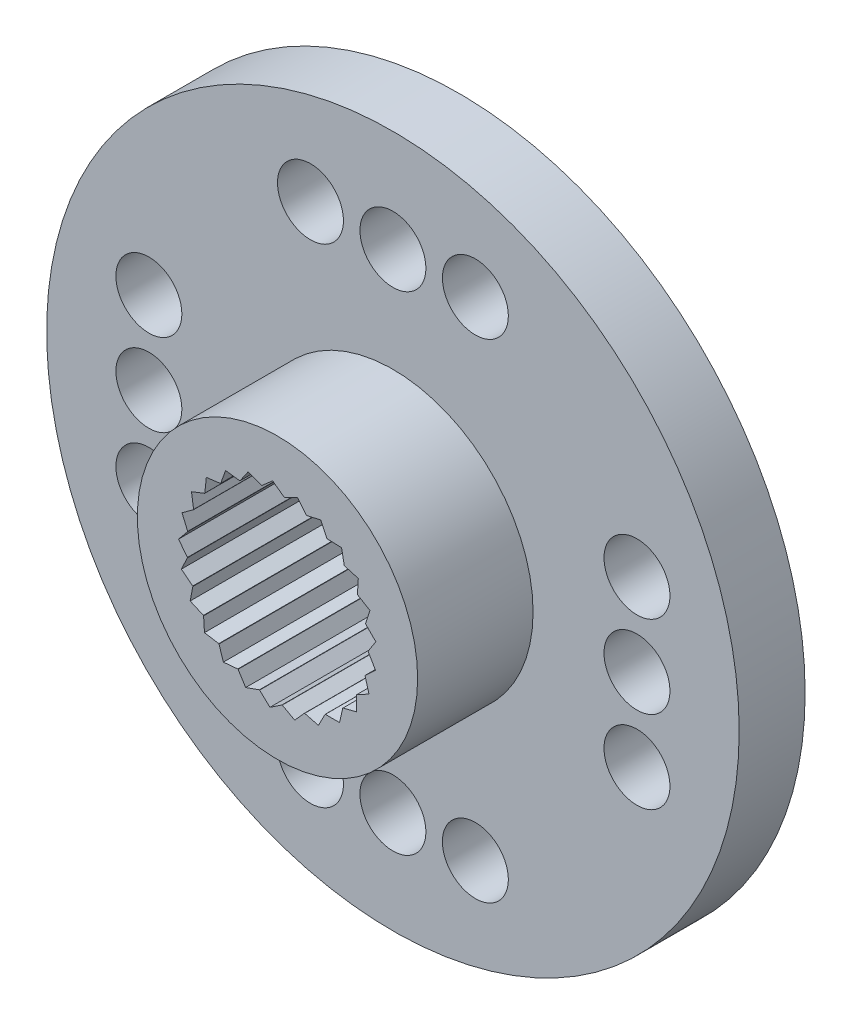
SolidWorks part; units mm, degrees
ref_plane "Front Plane" through (0, 0, 0) normal (0, 0, 1) x (1, 0, 0)
ref_plane "Top Plane" through (0, 0, 0) normal (0, 1, 0) x (1, 0, 0)
ref_plane "Right Plane" through (0, 0, 0) normal (1, 0, 0) x (0, 0, -1)
sketch "Sketch1" plane through (0, 0, 0) normal (0, 0, 1) x (1, 0, 0)
  circle A0 centre (0, 0) radius 10.5
  dimension "D1" = 21
extrude "Boss-Extrude1" add sketch "Sketch1" along normal blind 2
sketch "Sketch2" plane through (0, 0, 2) normal (0, 0, 1) x (1, 0, 0)
  circle A0 centre (0, 0) radius 4.25
  dimension "D1" = 8.5
extrude "Boss-Extrude2" add sketch "Sketch2" along normal blind 3.5
sketch "Sketch3" plane through (0, 0, 5.5) normal (0, 0, 1) x (1, 0, 0)
  circle A0 centre (0, 0) radius 2.75
  dimension "D1" = 5.5
extrude "Cut-Extrude1" cut sketch "Sketch3" against normal blind 4.5
sketch "Sketch4" plane through (0, 0, 0) normal (0, 0, 1) x (1, 0, 0)
  circle A0 centre (0, 0) radius 1.6
  dimension "D1" = 3.2
extrude "Cut-Extrude2" cut sketch "Sketch4" along normal blind 3.5
sketch "Sketch5" plane through (0, 0, 2) normal (0, 0, 1) x (1, 0, 0)
  line L0 (-10.5, 0) -> (10.5, 0) construction
  line L1 (-2.5, 7.4) -> (0, 7.4) construction
  line L2 (0, 7.4) -> (2.5, 7.4) construction
  line L3 (0, 7.4) -> (0, 0) construction
  line L4 (0, -7.4) -> (2.5, -7.4) construction
  line L5 (-2.5, -7.4) -> (0, -7.4) construction
  line L6 (7.4, 2.5) -> (7.4, 0) construction
  line L7 (7.4, 0) -> (7.4, -2.5) construction
  line L8 (-7.4, 0) -> (-7.4, -2.5) construction
  line L9 (-7.4, 2.5) -> (-7.4, 0) construction
  circle A0 centre (0, 7.4) radius 1
  circle A1 centre (-2.5, 7.4) radius 1
  circle A2 centre (2.5, 7.4) radius 1
  circle A3 centre (0, 0) radius 10.5 construction
  circle A4 centre (2.5, -7.4) radius 1
  circle A5 centre (-2.5, -7.4) radius 1
  circle A6 centre (0, -7.4) radius 1
  circle A7 centre (7.4, 0) radius 1
  circle A8 centre (7.4, 2.5) radius 1
  circle A9 centre (7.4, -2.5) radius 1
  circle A10 centre (-7.4, -2.5) radius 1
  circle A11 centre (-7.4, 2.5) radius 1
  circle A12 centre (-7.4, 0) radius 1
  dimension "D1" = 2
  dimension "D2" = 2
  dimension "D3" = 2
  dimension "D7" = 2
  dimension "D8" = 2
  dimension "D9" = 2
  dimension "D4" = 2.5
  dimension "D5" = 2.5
  dimension "D6" = 7.4
  dimension "D10" = 2.5
  dimension "D11" = 2.5
  dimension "D12" = 7.4
extrude "Cut-Extrude3" cut sketch "Sketch5" against normal blind 3.5
sketch "Sketch6" plane through (0, 0, 5.5) normal (0, 0, 1) x (1, 0, 0)
  line L0 (-0.9385, 2.5849) -> (-1.5278, 2.371)
  line L1 (0, 0) -> (-2.971, 0.4161)
  line L2 (0, 0) -> (-2.8954, 0.7852)
  line L3 (-2.8954, 0.7852) -> (-2.7234, 0.3814)
  line L4 (-2.8954, 0.7852) -> (-2.5466, 1.0378)
  line L5 (0, 0) -> (-2.7782, 1.1322)
  circle A0 centre (0, 0) radius 2.75
  circle A1 centre (0, 0) radius 2.75 construction
  circle A2 centre (0, 0) radius 3
  point P12 (0, 0)
  point P14 (-2.5929, 1.0567)
  circle M4 centre (0, 0) radius 2.75
  dimension "D3" = 6
  dimension "D1" = 7.2
  dimension "D2" = 14.2
extrude "Cut-Extrude4" cut sketch "Sketch6" against normal blind 4.5 contours L4 L2 M4 | L2 L3 M4
pattern_circular "CirPattern1" count 25 over 360 about axis through (0, 0, 0) along (0, 0, 1) of "Cut-Extrude4"
